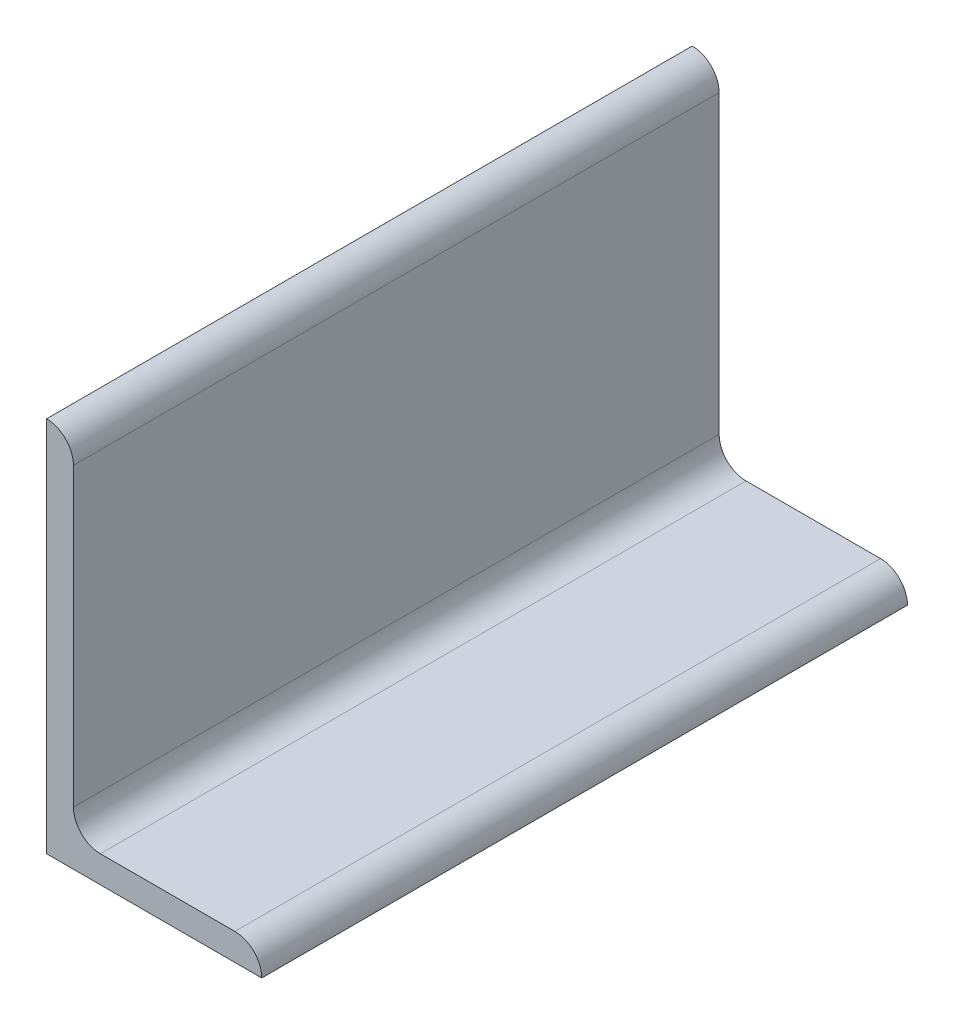
SolidWorks part; units mm, degrees
ref_plane "Front Plane" through (0, 0, 0) normal (0, 0, 1) x (1, 0, 0)
ref_plane "Top Plane" through (0, 0, 0) normal (0, 1, 0) x (1, 0, 0)
ref_plane "Right Plane" through (0, 0, 0) normal (1, 0, 0) x (0, 0, -1)
sketch "Sketch2" plane through (0, 0, 0) normal (0, 0, 1) x (1, 0, 0)
  line L0 (0, 0) -> (0, 177.8)
  line L1 (0, 177.8) -> (0.0051, 177.8)
  line L2 (12.7, 165.1051) -> (12.7, 25.4)
  line L3 (25.4, 12.7) -> (88.9051, 12.7)
  line L4 (101.6, 0.0051) -> (101.6, 0)
  line L5 (101.6, 0) -> (0, 0)
  arc A0 (101.6, 0.0051) -> (88.9051, 12.7) centre (88.9051, 0.0051) ccw
  arc A1 (0.0051, 177.8) -> (12.7, 165.1051) centre (0.0051, 165.1051) cw
  arc A2 (25.4, 12.7) -> (12.7, 25.4) centre (25.4, 25.4) cw
  circle A3 centre (0, 0) radius 12.7 construction
  dimension "D2" = 0.0051
  dimension "Radius_1" = 12.7
  dimension "Radius_2" = 12.7
  dimension "D1" = 12.7
  dimension "V_leg" = 177.8
  dimension "H_leg" = 101.6
  dimension "Thickness" = 12.7
  dimension "Flat_wid" = 0.0051
extrude "Boss-Extrude2" add sketch "Sketch2" along normal mid plane 304.8
